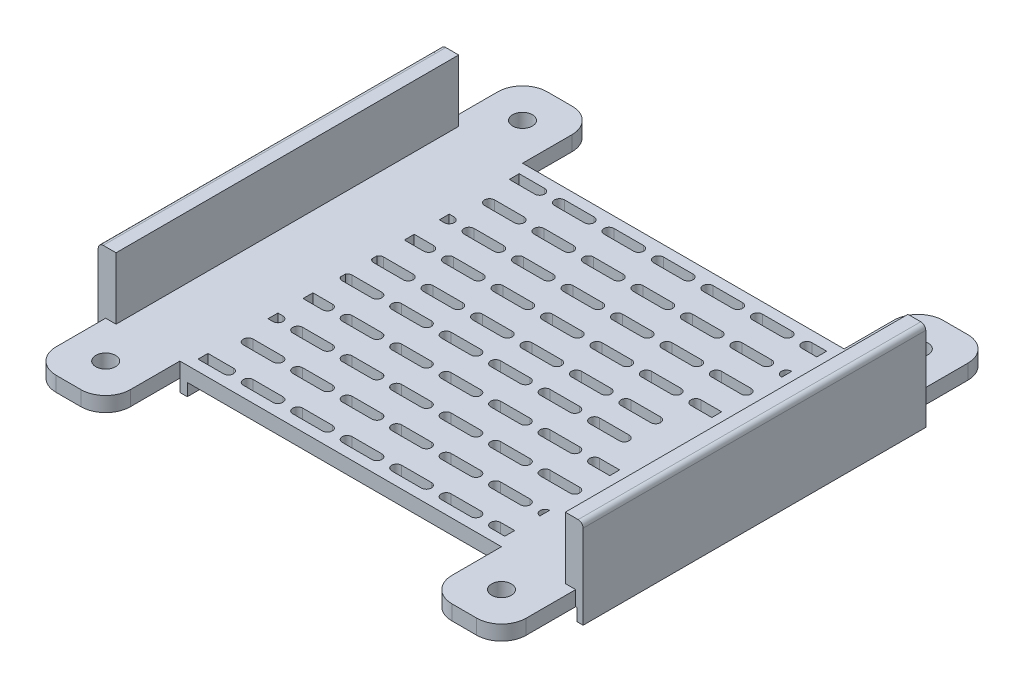
SolidWorks part; units mm, degrees
ref_plane "前视基准面" through (0, 0, 0) normal (0, 0, 1) x (1, 0, 0)
ref_plane "上视基准面" through (0, 0, 0) normal (0, 1, 0) x (1, 0, 0)
ref_plane "右视基准面" through (0, 0, 0) normal (1, 0, 0) x (0, 0, -1)
sketch "草图1" plane through (0, 0, 0) normal (0, 1, 0) x (1, 0, 0)
  line L0 (95.5, 69.25) -> (95.5, -69.25)
  line L1 (90.5, 64.25) -> (-90.5, 64.25)
  line L2 (90.5, 64.25) -> (90.5, -64.25)
  line L3 (90.5, -64.25) -> (-90.5, -64.25)
  line L4 (-90.5, 64.25) -> (-90.5, -64.25)
  line L5 (90.5, 64.25) -> (-90.5, -64.25) construction
  line L6 (90.5, -64.25) -> (-90.5, 64.25) construction
  line L7 (95.5, -69.25) -> (-95.5, -69.25)
  line L8 (-95.5, 69.25) -> (-95.5, -69.25)
  line L9 (95.5, 69.25) -> (-95.5, 69.25)
  point P0 (0, 0)
  dimension "D1" = 5
extrude "凸台-拉伸1" add sketch "草图1" along normal blind 20
sketch "草图2" plane through (0, 0, 0) normal (0, -1, 0) x (1, 0, 0)
  line L4 (-95.5, -69.25) -> (95.5, -69.25)
  line L5 (95.5, -69.25) -> (95.5, 69.25)
  line L6 (95.5, 69.25) -> (-95.5, 69.25)
  line L7 (-95.5, 69.25) -> (-95.5, -69.25)
  line L8 (-95.5, -69.25) -> (95.5, -69.25)
  line L9 (95.5, -69.25) -> (95.5, 69.25)
  line L10 (95.5, 69.25) -> (-95.5, 69.25)
  line L11 (-95.5, 69.25) -> (-95.5, -69.25)
  dimension "D1" = 0
extrude "凸台-拉伸2" add sketch "草图2" along normal blind 5
sketch "草图3" plane through (0, 0, -64.25) normal (0, 0, 1) x (1, 0, 0)
  line L4 (-90.5, 0) -> (90.5, 0)
  line L5 (90.5, 0) -> (90.5, 20)
  line L6 (90.5, 20) -> (-90.5, 20)
  line L7 (-90.5, 20) -> (-90.5, 0)
  line L8 (-90.5, 0) -> (90.5, 0)
  line L9 (90.5, 0) -> (90.5, 20)
  line L10 (90.5, 20) -> (-90.5, 20)
  line L11 (-90.5, 20) -> (-90.5, 0)
  dimension "D1" = 0
extrude "切除-拉伸1" cut sketch "草图3" against normal blind 49 and the other way blind 153
sketch "草图4" plane through (0, -5, 0) normal (0, -1, 0) x (1, 0, 0)
  line L0 (-95.5, 0) -> (-47.5, 0) construction
  line L1 (-47.5, 103) -> (47.5, 103) construction
  line L2 (-47.5, 103) -> (-47.5, -103) construction
  line L3 (-47.5, -103) -> (47.5, -103) construction
  line L4 (47.5, 103) -> (47.5, -103) construction
  line L5 (-47.5, 103) -> (47.5, -103) construction
  line L6 (-47.5, -103) -> (47.5, 103) construction
  line L7 (-95.5, 69.25) -> (-95.5, -69.25) construction
  line L8 (-95.5, 0) -> (-95.5, -35)
  line L9 (-95.5, -35) -> (-90.5, -35)
  line L10 (-90.5, -35) -> (-90.5, 35)
  line L11 (-90.5, 35) -> (-95.5, 35)
  line L12 (-95.5, 35) -> (-95.5, 0)
  line L13 (0, 0) -> (0, 35) construction
  line L14 (95.5, 35) -> (95.5, 0)
  line L15 (90.5, 35) -> (95.5, 35)
  line L16 (90.5, -35) -> (90.5, 35)
  line L17 (95.5, -35) -> (90.5, -35)
  line L18 (95.5, 0) -> (95.5, -35)
  point P0 (0, 0)
extrude "凸台-拉伸3" add sketch "草图4" along normal blind 49
sketch "草图5" plane through (0, -54, 0) normal (0, -1, 0) x (1, 0, 0)
  line L4 (-95.5, 35) -> (-95.5, -35)
  line L5 (-95.5, -35) -> (-90.5, -35)
  line L6 (-90.5, -35) -> (-90.5, 35)
  line L7 (-90.5, 35) -> (-95.5, 35)
  line L8 (-95.5, 35) -> (-95.5, -35)
  line L9 (-95.5, -35) -> (-90.5, -35)
  line L10 (-90.5, -35) -> (-90.5, 35)
  line L11 (-90.5, 35) -> (-95.5, 35)
  line L12 (95.5, 35) -> (90.5, 35)
  line L13 (90.5, 35) -> (90.5, -35)
  line L14 (90.5, -35) -> (95.5, -35)
  line L15 (95.5, -35) -> (95.5, 35)
  line L16 (95.5, 35) -> (90.5, 35)
  line L17 (90.5, 35) -> (90.5, -35)
  line L18 (90.5, -35) -> (95.5, -35)
  line L19 (95.5, -35) -> (95.5, 35)
  dimension "D1" = 0
  dimension "D2" = 0
extrude "凸台-拉伸4" add sketch "草图5" along normal blind 34
sketch "草图7" plane through (-95.5, 0, 0) normal (-1, 0, 0) x (0, 0, 1)
  line L0 (35, -88) -> (-35, -88)
  line L1 (-35, -88) -> (-35, -83)
  line L2 (-35, -88) -> (-35, -5) construction
  line L3 (-35, -83) -> (35, -83)
  line L4 (35, -88) -> (35, -5) construction
  line L5 (35, -83) -> (35, -88)
extrude "凸台-拉伸5" add sketch "草图7" along normal blind 37
sketch "草图8" plane through (95.5, 0, 0) normal (1, 0, 0) x (0, 0, -1)
  line L4 (-35, -83) -> (-35, -88)
  line L5 (35, -83) -> (-35, -83)
  line L6 (35, -88) -> (35, -83)
  line L7 (-35, -88) -> (35, -88)
  line L8 (-35, -83) -> (-35, -88)
  line L9 (35, -83) -> (-35, -83)
  line L10 (35, -88) -> (35, -83)
  line L11 (-35, -88) -> (35, -88)
  dimension "D1" = 0
extrude "凸台-拉伸6" add sketch "草图8" along normal blind 37
sketch "草图12" plane through (0, -5, 0) normal (0, -1, 0) x (1, 0, 0)
  line L0 (0, 0) -> (0, -50.9491) construction
  line L1 (0, 0) -> (21.7152, 0) construction
  line L6 (90.5, 35) -> (95.5, 35)
  line L7 (90.5, 35) -> (95.5, 35)
  line L8 (95.5, -69.25) -> (95.5, -35)
  line L9 (95.5, -35) -> (90.5, -35)
  line L10 (90.5, -35) -> (90.5, 35)
  line L11 (95.5, 35) -> (95.5, 69.25)
  line L15 (95.5, -35) -> (90.5, -35) construction
  line L16 (90.5, -35) -> (90.5, 35) construction
  line L20 (95.5, -69.25) -> (95.5, -35)
  line L27 (95.5, 35) -> (95.5, 69.25)
  line L28 (95.5, 69.25) -> (-95.5, 69.25)
  line L29 (95.5, 69.25) -> (-95.5, 69.25)
  line L30 (-95.5, 69.25) -> (-95.5, 35)
  line L31 (-95.5, 69.25) -> (-95.5, 35)
  line L32 (-95.5, 35) -> (-90.5, 35)
  line L33 (-95.5, 35) -> (-90.5, 35)
  line L34 (-90.5, 35) -> (-90.5, -35)
  line L35 (-90.5, 35) -> (-90.5, -35)
  line L36 (-90.5, -35) -> (-95.5, -35)
  line L37 (-90.5, -35) -> (-95.5, -35)
  line L38 (-95.5, -35) -> (-95.5, -69.25)
  line L39 (-95.5, -35) -> (-95.5, -69.25)
  line L40 (-95.5, -69.25) -> (95.5, -69.25)
  line L41 (-95.5, -69.25) -> (95.5, -69.25)
  circle A0 centre (48, -35) radius 12.5
  circle A1 centre (-48, -35) radius 12.5
  circle A2 centre (48, 35) radius 12.5
  circle A3 centre (-48, 35) radius 12.5
  dimension "D1" = 0
sketch "草图16" plane through (0, -88, 0) normal (0, -1, 0) x (1, 0, 0)
  line L0 (132.5, 35) -> (117.5, 35)
  line L1 (132.5, 35) -> (90.5, 35) construction
  line L2 (117.5, 35) -> (117.5, -35)
  line L3 (90.5, -35) -> (132.5, -35) construction
  line L4 (117.5, -35) -> (132.5, -35)
  line L5 (132.5, -35) -> (132.5, 35)
  line L6 (-132.5, -35) -> (-117.5, -35)
  line L7 (-132.5, -35) -> (-90.5, -35) construction
  line L8 (-117.5, -35) -> (-117.5, 35)
  line L9 (-90.5, 35) -> (-132.5, 35) construction
  line L10 (-117.5, 35) -> (-132.5, 35)
  line L11 (-132.5, 35) -> (-132.5, -35)
extrude "切除-拉伸7" cut sketch "草图16" against normal blind 62
extrude "切除-拉伸9" cut sketch "草图12" against normal blind 20 contours A0 | A1 | A3 | A2
sketch "草图19" plane through (117.5, 0, 0) normal (1, 0, 0) x (0, 0, -1)
  line L4 (-35, -83) -> (-35, -88)
  line L5 (-35, -88) -> (35, -88)
  line L6 (35, -88) -> (35, -83)
  line L7 (35, -83) -> (-35, -83)
  line L8 (-35, -83) -> (-35, -88)
  line L9 (-35, -88) -> (35, -88)
  line L10 (35, -88) -> (35, -83)
  line L11 (35, -83) -> (-35, -83)
  dimension "D1" = 0
extrude "切除-拉伸10" cut sketch "草图19" against normal blind 3.5
sketch "草图20" plane through (-117.5, 0, 0) normal (-1, 0, 0) x (0, 0, 1)
  line L4 (-35, -83) -> (-35, -88)
  line L5 (-35, -88) -> (35, -88)
  line L6 (35, -88) -> (35, -83)
  line L7 (35, -83) -> (-35, -83)
  line L8 (-35, -83) -> (-35, -88)
  line L9 (-35, -88) -> (35, -88)
  line L10 (35, -88) -> (35, -83)
  line L11 (35, -83) -> (-35, -83)
  dimension "D1" = 0
extrude "切除-拉伸11" cut sketch "草图20" against normal blind 3.5
sketch "草图21" plane through (0, -83, 0) normal (0, 1, 0) x (1, 0, 0)
  line L0 (-114, 0) -> (-95.5, 0) construction
  line L1 (-114, -35) -> (-114, 35) construction
  line L2 (-95.5, -35) -> (-95.5, 35) construction
  line L3 (-104.75, 0) -> (-104.75, -35) construction
  line L4 (-114, -35) -> (-95.5, -35) construction
  line L5 (0, 0) -> (0, 27.7926) construction
  circle A0 centre (-104.75, -17.5) radius 4
  circle A1 centre (-104.75, 17.5) radius 4
  circle A2 centre (104.75, -17.5) radius 4
  circle A3 centre (104.75, 17.5) radius 4
extrude "切除-拉伸12" cut sketch "草图21" against normal through all
fillet "圆角5" radius 10 4 edges at (114, -85.5, -35) (114, -85.5, 35) (-114, -85.5, 35) (-114, -85.5, -35)
sketch "草图22" plane through (90.5, 0, 0) normal (-1, 0, 0) x (0, 0, 1)
  line L6 (35, -88) -> (35, -5)
  line L7 (35, -5) -> (-35, -5)
  line L10 (-35, -5) -> (-35, -88)
  line L11 (-35, -88) -> (35, -88)
  line L12 (35, -88) -> (35, -5)
  line L13 (35, -5) -> (-35, -5)
  line L16 (-35, -5) -> (-35, -88)
  line L17 (-35, -88) -> (35, -88)
  dimension "D1" = 0
extrude "切除-拉伸13" cut sketch "草图22" against normal blind 54
sketch "草图23" plane through (-90.5, 0, 0) normal (1, 0, 0) x (0, 0, -1)
  line L6 (35, -5) -> (-35, -5)
  line L7 (-35, -5) -> (-35, -88)
  line L8 (-35, -88) -> (35, -88)
  line L9 (35, -88) -> (35, -5)
  line L12 (35, -5) -> (-35, -5)
  line L13 (-35, -5) -> (-35, -88)
  line L14 (-35, -88) -> (35, -88)
  line L15 (35, -88) -> (35, -5)
  dimension "D1" = 0
extrude "切除-拉伸14" cut sketch "草图23" against normal blind 54
sketch "草图24" plane through (0, -5, 0) normal (0, -1, 0) x (1, 0, 0)
  circle A1 centre (80.5, 18.25) radius 2
  circle A3 centre (80.5, -19.75) radius 2
extrude "切除-拉伸15" cut sketch "草图24" against normal blind 10
sketch "草图25" plane through (0, 0, 0) normal (0, 1, 0) x (1, 0, 0)
  circle A0 centre (80.5, -18.25) radius 4
  circle A1 centre (80.5, 19.75) radius 4
sketch "草图26" plane through (0, 0, 0) normal (0, 1, 0) x (1, 0, 0)
  line L4 (90.5, -69.25) -> (90.5, 69.25)
  line L5 (90.5, 69.25) -> (-90.5, 69.25)
  line L6 (-90.5, 69.25) -> (-90.5, -69.25)
  line L7 (-90.5, -69.25) -> (90.5, -69.25)
  line L8 (90.5, -69.25) -> (90.5, 69.25)
  line L9 (90.5, 69.25) -> (-90.5, 69.25)
  line L10 (-90.5, 69.25) -> (-90.5, -69.25)
  line L11 (-90.5, -69.25) -> (90.5, -69.25)
  circle A0 centre (48, -35) radius 12.5 construction
  circle A1 centre (48, -35) radius 12.5
  circle A2 centre (48, 35) radius 12.5 construction
  circle A3 centre (48, 35) radius 12.5
  circle A4 centre (-48, -35) radius 12.5 construction
  circle A5 centre (-48, -35) radius 12.5
  circle A6 centre (-48, 35) radius 12.5 construction
  circle A7 centre (-48, 35) radius 12.5
  dimension "D1" = 0
extrude "凸台-拉伸8" add sketch "草图26" along normal blind 1
extrude "切除-拉伸16" cut sketch "草图25" along normal blind 1 and the other way blind 4
mirror "镜向1" about plane through (0, 0, 0) normal (1, 0, 0) of "切除-拉伸15", "切除-拉伸16"
sketch "草图28" plane through (0, 1, 0) normal (0, 1, 0) x (1, 0, 0)
  circle A0 centre (-80.5, -18.25) radius 4 construction
  circle A1 centre (-80.5, -18.25) radius 4
  circle A2 centre (-80.5, 19.75) radius 4 construction
  circle A3 centre (-80.5, 19.75) radius 4
  circle A4 centre (80.5, -18.25) radius 4 construction
  circle A5 centre (80.5, -18.25) radius 4
  circle A6 centre (80.5, 19.75) radius 4 construction
  circle A7 centre (80.5, 19.75) radius 4
extrude "凸台-拉伸9" add sketch "草图28" against normal up to surface (6 mm away) up to face at (-80.5, -5, 16.25)
sketch "草图29" plane through (0, -5, 0) normal (0, -1, 0) x (1, 0, 0)
  line L0 (95.5, 69.25) -> (95, 69.25)
  line L1 (-95, 0) -> (-95, 69.25)
  line L2 (95.5, 69.25) -> (-95.5, 69.25) construction
  line L3 (-95, 69.25) -> (-95.5, 69.25)
  line L4 (-95.5, 69.25) -> (-95.5, -69.25)
  line L5 (-95.5, -69.25) -> (-95, -69.25)
  line L6 (-95.5, -69.25) -> (95.5, -69.25) construction
  line L7 (-95, -69.25) -> (-95, 0)
  line L8 (95, 69.25) -> (95, -69.25)
  line L9 (95, -69.25) -> (95.5, -69.25)
  line L10 (95.5, -69.25) -> (95.5, 69.25)
extrude "切除-拉伸18" cut sketch "草图29" against normal blind 50
sketch "草图31" plane through (0, -5, 0) normal (0, -1, 0) x (1, 0, 0)
  line L0 (-95, 69.25) -> (-95, 89.25)
  line L1 (-85, 99.25) -> (-75, 99.25)
  line L2 (-65, 89.25) -> (-65, 69.25)
  line L3 (95, 69.25) -> (-95, 69.25) construction
  line L4 (-65, 69.25) -> (-95, 69.25)
  line L5 (-80, 99.25) -> (-80, 69.25) construction
  line L6 (-80, 84.25) -> (-65, 84.25) construction
  line L7 (0, 0) -> (19.0311, 0) construction
  line L8 (0, 0) -> (0, -16.3488) construction
  line L9 (-65, -89.25) -> (-65, -69.25)
  line L10 (-85, -99.25) -> (-75, -99.25)
  line L11 (-95, -69.25) -> (-95, -89.25)
  line L12 (-65, -69.25) -> (-95, -69.25)
  line L13 (80, 84.25) -> (65, 84.25) construction
  line L14 (80, 99.25) -> (80, 69.25) construction
  line L15 (65, -69.25) -> (95, -69.25)
  line L16 (95, -69.25) -> (95, -89.25)
  line L17 (85, -99.25) -> (75, -99.25)
  line L18 (65, -89.25) -> (65, -69.25)
  line L19 (65, 69.25) -> (95, 69.25)
  line L20 (65, 89.25) -> (65, 69.25)
  line L21 (85, 99.25) -> (75, 99.25)
  line L22 (95, 69.25) -> (95, 89.25)
  arc A0 (-65, 89.25) -> (-75, 99.25) centre (-75, 89.25) ccw
  arc A1 (-95, 89.25) -> (-85, 99.25) centre (-85, 89.25) cw
  circle A2 centre (-80, 84.25) radius 4
  circle A3 centre (-80, -84.25) radius 4
  arc A4 (-65, -89.25) -> (-75, -99.25) centre (-75, -89.25) cw
  arc A5 (-95, -89.25) -> (-85, -99.25) centre (-85, -89.25) ccw
  arc A6 (95, -89.25) -> (85, -99.25) centre (85, -89.25) cw
  arc A7 (65, -89.25) -> (75, -99.25) centre (75, -89.25) ccw
  circle A8 centre (80, -84.25) radius 4
  circle A9 centre (80, 84.25) radius 4
  arc A10 (95, 89.25) -> (85, 99.25) centre (85, 89.25) ccw
  arc A11 (65, 89.25) -> (75, 99.25) centre (75, 89.25) cw
  dimension "D1" = 10
extrude "凸台-拉伸10" add sketch "草图31" against normal up to surface (6 mm away) up to face at (-48, 1, 47.5)
sketch "草图32" plane through (0, 20, 0) normal (0, 1, 0) x (1, 0, 0)
  line L0 (90.5, 69.25) -> (91.3, 69.25)
  line L4 (95, 69.25) -> (90.5, 69.25) construction
  line L5 (90.5, -69.25) -> (90.5, 69.25) construction
  line L6 (90.5, -69.25) -> (90.5, 69.25)
  line L7 (91.3, 69.25) -> (91.3, -69.25)
  line L8 (90.5, -69.25) -> (95, -69.25) construction
  line L9 (91.3, -69.25) -> (90.5, -69.25)
  line L10 (-90.5, -69.25) -> (-91.3, -69.25)
  line L11 (-95, -69.25) -> (-90.5, -69.25) construction
  line L12 (-91.3, -69.25) -> (-91.3, 69.25)
  line L13 (-90.5, 69.25) -> (-95, 69.25) construction
  line L14 (-91.3, 69.25) -> (-90.5, 69.25)
  line L15 (-90.5, 69.25) -> (-90.5, -69.25) construction
  line L16 (-90.5, 69.25) -> (-90.5, -69.25)
extrude "切除-拉伸19" cut sketch "草图32" against normal up to surface (19 mm away) up to face at (-48, 1, 47.5)
sketch "草图33" plane through (0, 20, 0) normal (0, 1, 0) x (1, 0, 0)
  line L4 (91.3, 69.25) -> (91.3, -69.25)
  line L5 (91.3, -69.25) -> (95, -69.25)
  line L6 (95, -69.25) -> (95, 69.25)
  line L7 (95, 69.25) -> (91.3, 69.25)
  line L8 (91.3, 69.25) -> (91.3, -69.25)
  line L9 (91.3, -69.25) -> (95, -69.25)
  line L10 (95, -69.25) -> (95, 69.25)
  line L11 (95, 69.25) -> (91.3, 69.25)
  line L12 (-91.3, -69.25) -> (-91.3, 69.25)
  line L13 (-91.3, 69.25) -> (-95, 69.25)
  line L14 (-95, 69.25) -> (-95, -69.25)
  line L15 (-95, -69.25) -> (-91.3, -69.25)
  line L16 (-91.3, -69.25) -> (-91.3, 69.25)
  line L17 (-91.3, 69.25) -> (-95, 69.25)
  line L18 (-95, 69.25) -> (-95, -69.25)
  line L19 (-95, -69.25) -> (-91.3, -69.25)
  dimension "D1" = 0
  dimension "D2" = 0
extrude "凸台-拉伸11" add sketch "草图33" along normal blind 6
sketch "草图34" plane through (0, -5, 0) normal (0, -1, 0) x (1, 0, 0)
  circle A0 centre (-48, -35) radius 12.5 construction
  circle A1 centre (-48, -35) radius 12.5
  circle A2 centre (-48, 35) radius 12.5 construction
  circle A3 centre (-48, 35) radius 12.5
  circle A4 centre (48, -35) radius 12.5 construction
  circle A5 centre (48, -35) radius 12.5
  circle A6 centre (48, 35) radius 12.5 construction
  circle A7 centre (48, 35) radius 12.5
extrude "凸台-拉伸12" add sketch "草图34" against normal up to surface (6 mm away) up to face at (0, 1, 0)
sketch "草图35" plane through (0, -5, 0) normal (0, -1, 0) x (1, 0, 0)
  line L0 (65, -69.25) -> (62, -69.25)
  line L2 (65, 69.25) -> (65, -69.25)
  line L6 (-65, -69.25) -> (65, -69.25) construction
  line L8 (62, -69.25) -> (62, 69.25)
  line L9 (65, 69.25) -> (-65, 69.25) construction
  line L10 (62, 69.25) -> (65, 69.25)
  line L11 (-65, -69.25) -> (-62, -69.25)
  line L12 (-62, -69.25) -> (-62, 69.25)
  line L13 (-62, 69.25) -> (-65, 69.25)
  line L14 (-65, 69.25) -> (-65, 89.25) construction
  line L15 (-65, 69.25) -> (-65, -69.25)
  point P0 (0, 0)
extrude "凸台-拉伸13" add sketch "草图35" along normal blind 5
sketch "草图36" plane through (-95, 0, 0) normal (-1, 0, 0) x (0, 0, 1)
  line L0 (-69.25, -10) -> (-69.25, -5) construction
  line L1 (-69.25, -10) -> (-69.25, -5)
  line L2 (69.25, -10) -> (69.25, -5) construction
  line L3 (69.25, -10) -> (69.25, -5)
  line L7 (-69.25, 26) -> (69.25, 26) construction
  line L8 (-69.25, 26) -> (69.25, 26)
  line L9 (69.25, 26) -> (69.25, 1) construction
  line L10 (69.25, 26) -> (69.25, 1)
  line L13 (-69.25, -10) -> (69.25, -10)
  line L16 (-69.25, 26) -> (-69.25, 1) construction
  line L17 (-69.25, 26) -> (-69.25, 1)
  line L18 (-69.25, 1) -> (-69.25, -5)
  line L19 (69.25, -5) -> (69.25, 1)
extrude "凸台-拉伸14" add sketch "草图36" along normal blind 3
sketch "草图37" plane through (-95, 0, 0) normal (1, 0, 0) x (0, 0, -1)
  line L4 (69.25, -5) -> (-69.25, -5)
  line L5 (-69.25, -5) -> (-69.25, -10)
  line L6 (-69.25, -10) -> (69.25, -10)
  line L7 (69.25, -10) -> (69.25, -5)
  line L8 (69.25, -5) -> (-69.25, -5)
  line L9 (-69.25, -5) -> (-69.25, -10)
  line L10 (-69.25, -10) -> (69.25, -10)
  line L11 (69.25, -10) -> (69.25, -5)
  dimension "D1" = 0
extrude "切除-拉伸20" cut sketch "草图37" against normal blind 0.5
mirror "镜向2" about plane through (0, 0, 0) normal (1, 0, 0) of "切除-拉伸20", "凸台-拉伸14"
sketch "草图38" plane through (0, -5, 0) normal (0, -1, 0) x (1, 0, 0)
  line L2 (0, 0) -> (62, 0)
  line L3 (62, 69.25) -> (62, -69.25) construction
  line L4 (0, -2.5) -> (-62, -2.5)
  line L5 (0, -2.5) -> (62, -2.5)
  line L6 (0, 2.5) -> (-62, 2.5)
  line L7 (0, 2.5) -> (62, 2.5)
  line L8 (-62, -69.25) -> (-62, 69.25) construction
  line L9 (-62, -2.5) -> (-62, 2.5)
  line L10 (62, 69.25) -> (62, -69.25) construction
  line L11 (62, 2.5) -> (62, -2.5)
  line L12 (0, 0) -> (-62, 0) construction
  dimension "D1" = 2.5
  dimension "D2" = 2.5
extrude "凸台-拉伸15" add sketch "草图38" along normal up to surface (5 mm away) contours L6 L9 L4 L5 L11 L7 up to face at (-63.5, -10, 0)
sketch "草图40" plane through (0, -5, 0) normal (0, -1, 0) x (1, 0, 0)
  line L0 (0, 0) -> (0, 69.25) construction
  line L1 (62, 69.25) -> (-62, 69.25) construction
  line L2 (0, 34.625) -> (-12, 34.625) construction
  line L3 (0, 34.625) -> (-32.125, 2.5) construction
  line L4 (0, 32.625) -> (-12, 32.625)
  line L5 (0, 36.625) -> (-12, 36.625)
  line L6 (62, 2.5) -> (-62, 2.5) construction
  line L7 (25, 34.625) -> (13, 34.625) construction
  line L8 (25, 32.625) -> (13, 32.625)
  line L9 (25, 36.625) -> (13, 36.625)
  line L10 (50, 34.625) -> (38, 34.625) construction
  line L11 (50, 32.625) -> (38, 32.625)
  line L12 (50, 36.625) -> (38, 36.625)
  line L13 (-25, 34.625) -> (-37, 34.625) construction
  line L14 (-25, 32.625) -> (-37, 32.625)
  line L15 (-25, 36.625) -> (-37, 36.625)
  arc A0 (0, 32.625) -> (0, 36.625) centre (0, 34.625) ccw
  arc A1 (-12, 36.625) -> (-12, 32.625) centre (-12, 34.625) ccw
  arc A2 (25, 32.625) -> (25, 36.625) centre (25, 34.625) ccw
  arc A3 (13, 36.625) -> (13, 32.625) centre (13, 34.625) ccw
  arc A4 (50, 32.625) -> (50, 36.625) centre (50, 34.625) ccw
  arc A5 (38, 36.625) -> (38, 32.625) centre (38, 34.625) ccw
  arc A6 (-25, 32.625) -> (-25, 36.625) centre (-25, 34.625) ccw
  arc A7 (-37, 36.625) -> (-37, 32.625) centre (-37, 34.625) ccw
  point P9 (-6, 34.625)
  point P20 (19, 34.625)
  point P27 (44, 34.625)
  point P34 (-31, 34.625)
  dimension "D1" = 45
  dimension "D2" = 3
  dimension "D3" = 2
extrude "切除-拉伸22" cut sketch "草图40" against normal through all contours L5 A1 L4 A0
sketch "草图41" plane through (0, -5, 0) normal (0, -1, 0) x (1, 0, 0)
  line L0 (0, 0) -> (0, 69.25)
  line L1 (62, 69.25) -> (-62, 69.25) construction
  line L2 (0, 34.625) -> (-32.125, 2.5)
  line L3 (62, 2.5) -> (-62, 2.5) construction
  dimension "D1" = 45
pattern_linear "阵列(线性)1" count 3 spacing 20 along (-0.7071, 0, -0.7071) of "切除-拉伸22"
pattern_linear "阵列(线性)2" count 3 spacing 20 along (0.7071, 0, 0.7071) of "切除-拉伸22"
pattern_linear "阵列(线性)3" count 5 spacing 20 along (1, 0, 0) of "阵列(线性)2", "阵列(线性)1", "切除-拉伸22"
sketch "草图42" plane through (0, 1, 0) normal (0, 1, 0) x (1, 0, 0)
  line L0 (82.1421, -50.7671) -> (91.3, -50.7671) construction
  line L1 (82.1421, -50.7671) -> (91.3, -50.7671)
  line L2 (82.1421, -46.7671) -> (91.3, -46.7671) construction
  line L3 (82.1421, -46.7671) -> (91.3, -46.7671)
  line L4 (94.1421, -46.7671) -> (91.3, -46.7671) construction
  line L5 (94.1421, -46.7671) -> (91.3, -46.7671)
  line L6 (94.1421, -50.7671) -> (91.3, -50.7671) construction
  line L7 (94.1421, -50.7671) -> (91.3, -50.7671)
  line L8 (98, -64.9093) -> (96.2843, -64.9093) construction
  line L9 (98, -64.9093) -> (96.2843, -64.9093)
  line L10 (98, -60.9093) -> (96.2843, -60.9093) construction
  line L11 (98, -60.9093) -> (96.2843, -60.9093)
  line L12 (98, -64.9093) -> (98, -60.9093) construction
  line L13 (98, -64.9093) -> (98, -60.9093)
  line L14 (76.2843, -60.9093) -> (88.2843, -60.9093) construction
  line L15 (76.2843, -60.9093) -> (88.2843, -60.9093)
  line L16 (76.2843, -64.9093) -> (88.2843, -64.9093) construction
  line L17 (76.2843, -64.9093) -> (88.2843, -64.9093)
  line L20 (56.2843, -60.9093) -> (68.2843, -60.9093) construction
  line L21 (65, -60.9093) -> (68.2843, -60.9093)
  line L22 (56.2843, -64.9093) -> (68.2843, -64.9093) construction
  line L23 (65, -64.9093) -> (68.2843, -64.9093)
  line L26 (62.1421, -50.7671) -> (74.1421, -50.7671) construction
  line L27 (62.1421, -46.7671) -> (74.1421, -46.7671) construction
  line L28 (65, -50.7671) -> (74.1421, -50.7671)
  line L29 (65, -46.7671) -> (74.1421, -46.7671)
  line L30 (68, -32.625) -> (80, -32.625) construction
  line L31 (68, -36.625) -> (80, -36.625) construction
  line L32 (68, -32.625) -> (80, -32.625)
  line L33 (68, -36.625) -> (80, -36.625)
  line L34 (53.8579, -22.4829) -> (65.8579, -22.4829) construction
  line L35 (53.8579, -18.4829) -> (65.8579, -18.4829) construction
  line L37 (65, -22.4829) -> (65.8579, -22.4829)
  line L38 (65, -18.4829) -> (65.8579, -18.4829)
  line L44 (62, -64.9093) -> (65, -64.9093)
  line L45 (65, -64.9093) -> (65, -60.9093)
  line L46 (65, -60.9093) -> (62, -60.9093)
  line L47 (62, -60.9093) -> (62, -64.9093)
  line L48 (62, -64.9093) -> (65, -64.9093)
  line L49 (62.1421, -50.7671) -> (65, -50.7671)
  line L50 (65, -60.9093) -> (62, -60.9093)
  line L51 (62, -60.9093) -> (62, -64.9093)
  line L52 (65, -50.7671) -> (65, -46.7671)
  line L53 (65, -46.7671) -> (62.1421, -46.7671)
  line L54 (62, -46.7722) -> (62, -50.7621)
  line L55 (62.1421, -50.7671) -> (65, -50.7671)
  line L56 (62, -22.4829) -> (65, -22.4829)
  line L57 (65, -46.7671) -> (62.1421, -46.7671)
  line L58 (62, -46.7722) -> (62, -50.7621)
  line L59 (65, -22.4829) -> (65, -18.4829)
  line L60 (65, -18.4829) -> (62, -18.4829)
  line L61 (62, -18.4829) -> (62, -22.4829)
  line L62 (62, -22.4829) -> (65, -22.4829)
  line L64 (65, -18.4829) -> (62, -18.4829)
  line L65 (62, -18.4829) -> (62, -22.4829)
  arc A0 (82.1421, -46.7671) -> (82.1421, -50.7671) centre (82.1421, -48.7671) ccw construction
  arc A1 (82.1421, -46.7671) -> (82.1421, -50.7671) centre (82.1421, -48.7671) ccw
  arc A2 (95.5, -50.2355) -> (95.5, -47.2987) centre (94.1421, -48.7671) ccw construction
  arc A3 (95.5, -50.2355) -> (95.5, -47.2987) centre (94.1421, -48.7671) ccw
  arc A4 (95.5, -47.2987) -> (94.1421, -46.7671) centre (94.1421, -48.7671) ccw construction
  arc A5 (95.5, -47.2987) -> (94.1421, -46.7671) centre (94.1421, -48.7671) ccw
  arc A6 (94.1421, -50.7671) -> (95.5, -50.2355) centre (94.1421, -48.7671) ccw construction
  arc A7 (94.1421, -50.7671) -> (95.5, -50.2355) centre (94.1421, -48.7671) ccw
  arc A8 (96.2843, -60.9093) -> (96.2843, -64.9093) centre (96.2843, -62.9093) ccw construction
  arc A9 (96.2843, -60.9093) -> (96.2843, -64.9093) centre (96.2843, -62.9093) ccw
  arc A10 (88.2843, -64.9093) -> (88.2843, -60.9093) centre (88.2843, -62.9093) ccw construction
  arc A11 (88.2843, -64.9093) -> (88.2843, -60.9093) centre (88.2843, -62.9093) ccw
  arc A12 (76.2843, -60.9093) -> (76.2843, -64.9093) centre (76.2843, -62.9093) ccw construction
  arc A13 (76.2843, -60.9093) -> (76.2843, -64.9093) centre (76.2843, -62.9093) ccw
  arc A14 (68.2843, -64.9093) -> (68.2843, -60.9093) centre (68.2843, -62.9093) ccw construction
  arc A15 (68.2843, -64.9093) -> (68.2843, -60.9093) centre (68.2843, -62.9093) ccw
  arc A16 (74.1421, -50.7671) -> (74.1421, -46.7671) centre (74.1421, -48.7671) ccw construction
  arc A17 (74.1421, -50.7671) -> (74.1421, -46.7671) centre (74.1421, -48.7671) ccw
  arc A18 (68, -32.625) -> (68, -36.625) centre (68, -34.625) ccw construction
  arc A19 (80, -36.625) -> (80, -32.625) centre (80, -34.625) ccw construction
  arc A20 (68, -32.625) -> (68, -36.625) centre (68, -34.625) ccw
  arc A21 (80, -36.625) -> (80, -32.625) centre (80, -34.625) ccw
  arc A22 (65.8579, -22.4829) -> (65.8579, -18.4829) centre (65.8579, -20.4829) ccw construction
  arc A23 (65.8579, -22.4829) -> (65.8579, -18.4829) centre (65.8579, -20.4829) ccw
  arc A26 (62, -50.7621) -> (62.1421, -50.7671) centre (62.1421, -48.7671) ccw
  arc A27 (62.1421, -46.7671) -> (62, -46.7722) centre (62.1421, -48.7671) ccw
  arc A28 (62, -50.7621) -> (62.1421, -50.7671) centre (62.1421, -48.7671) ccw
  arc A29 (62.1421, -46.7671) -> (62, -46.7722) centre (62.1421, -48.7671) ccw
  dimension "D1" = 0
  dimension "D2" = 0
  dimension "D3" = 0
extrude "凸台-拉伸16" add sketch "草图42" against normal up to surface (6 mm away) up to face at (63.5, -5, 62.9093)
sketch "草图43" plane through (0, 1, 0) normal (0, 1, 0) x (1, 0, 0)
  line L0 (94.1421, -46.7671) -> (91.3, -46.7671) construction
  line L1 (94.1421, -46.7671) -> (91.3, -46.7671)
  line L2 (94.1421, -50.7671) -> (91.3, -50.7671) construction
  line L3 (96.2843, -64.9093) -> (98, -64.9093)
  line L4 (98, -64.9093) -> (98, -60.9093)
  line L5 (98, -60.9093) -> (96.2843, -60.9093)
  line L6 (96.2843, -64.9093) -> (98, -64.9093)
  line L7 (98, -64.9093) -> (98, -60.9093)
  line L8 (98, -60.9093) -> (96.2843, -60.9093)
  line L9 (94.1421, -50.7671) -> (91.3, -50.7671)
  line L10 (91.3, -50.7671) -> (91.3, -46.7671)
  arc A0 (94.1421, -50.7671) -> (94.1421, -46.7671) centre (94.1421, -48.7671) ccw construction
  arc A1 (96.2843, -60.9093) -> (96.2843, -64.9093) centre (96.2843, -62.9093) ccw
  arc A2 (96.2843, -60.9093) -> (96.2843, -64.9093) centre (96.2843, -62.9093) ccw
  arc A3 (94.1421, -50.7671) -> (94.1421, -46.7671) centre (94.1421, -48.7671) ccw
  dimension "D1" = 0
extrude "凸台-拉伸17" add sketch "草图43" along normal up to surface (25 mm away)
pattern_linear "阵列(线性)4" count 5 spacing 20 along (-1, 0, 0) of "阵列(线性)1", "阵列(线性)2", "切除-拉伸22"
sketch "草图44" plane through (0, 1, 0) normal (0, 1, 0) x (1, 0, 0)
  line L0 (-63.7157, -64.9093) -> (-51.7157, -64.9093) construction
  line L1 (-63.7157, -60.9093) -> (-51.7157, -60.9093) construction
  line L2 (-62, -60.9093) -> (-62, -64.9093) construction
  line L3 (-62, -32.625) -> (-62, -36.625) construction
  line L4 (-72, -32.625) -> (-60, -32.625) construction
  line L5 (-72, -36.625) -> (-60, -36.625) construction
  line L7 (-77.8579, -50.7671) -> (-65.8579, -50.7671) construction
  line L8 (-77.8579, -46.7671) -> (-65.8579, -46.7671) construction
  line L9 (-63.7157, -64.9093) -> (-62, -64.9093)
  line L10 (-63.7157, -60.9093) -> (-62, -60.9093)
  line L11 (-62, -60.9093) -> (-62, -64.9093)
  line L12 (-62, -32.625) -> (-62, -36.625)
  line L13 (-72, -32.625) -> (-62, -32.625)
  line L14 (-72, -36.625) -> (-62, -36.625)
  line L16 (-77.8579, -50.7671) -> (-65.8579, -50.7671)
  line L17 (-77.8579, -46.7671) -> (-65.8579, -46.7671)
  line L18 (-98, -4.3407) -> (-98, -8.3407) construction
  line L19 (-62, -18.4829) -> (-62, -22.4829) construction
  line L20 (-66.1421, -22.4829) -> (-54.1421, -22.4829) construction
  line L21 (-66.1421, -18.4829) -> (-54.1421, -18.4829) construction
  line L22 (-62, -5.313) -> (-62, -7.3685) construction
  line L23 (-80.2843, -8.3407) -> (-68.2843, -8.3407) construction
  line L24 (-80.2843, -4.3407) -> (-68.2843, -4.3407) construction
  line L25 (-91.3, -8.3407) -> (-88.2843, -8.3407) construction
  line L26 (-91.3, -4.3407) -> (-88.2843, -4.3407) construction
  line L27 (-91.3, -4.3407) -> (-98, -4.3407) construction
  line L28 (-91.3, -8.3407) -> (-98, -8.3407) construction
  line L29 (-98, -4.3407) -> (-98, -8.3407)
  line L30 (-91.3, -8.3407) -> (-98, -8.3407)
  line L31 (-91.3, -4.3407) -> (-98, -4.3407)
  line L32 (-91.3, -4.3407) -> (-88.2843, -4.3407)
  line L33 (-91.3, -8.3407) -> (-88.2843, -8.3407)
  line L34 (-80.2843, -4.3407) -> (-68.2843, -4.3407)
  line L35 (-80.2843, -8.3407) -> (-68.2843, -8.3407)
  line L36 (-62, -5.313) -> (-62, -7.3685)
  line L37 (-66.1421, -18.4829) -> (-62, -18.4829)
  line L38 (-66.1421, -22.4829) -> (-62, -22.4829)
  line L39 (-62, -18.4829) -> (-62, -22.4829)
  line L40 (-91.3, -36.625) -> (-80, -36.625) construction
  line L41 (-92, -36.625) -> (-91.3, -36.625) construction
  line L42 (-92, -32.625) -> (-91.3, -32.625) construction
  line L43 (-91.3, -32.625) -> (-80, -32.625) construction
  line L44 (-86.1421, -22.4829) -> (-74.1421, -22.4829) construction
  line L45 (-86.1421, -18.4829) -> (-74.1421, -18.4829) construction
  line L46 (-94.1421, -22.4829) -> (-98, -22.4829) construction
  line L47 (-94.1421, -18.4829) -> (-98, -18.4829) construction
  line L48 (-98, -18.4829) -> (-98, -22.4829) construction
  line L49 (-91.3, -36.625) -> (-80, -36.625)
  line L50 (-92, -36.625) -> (-91.3, -36.625)
  line L51 (-92, -32.625) -> (-91.3, -32.625)
  line L52 (-91.3, -32.625) -> (-80, -32.625)
  line L53 (-86.1421, -22.4829) -> (-74.1421, -22.4829)
  line L54 (-86.1421, -18.4829) -> (-74.1421, -18.4829)
  line L55 (-94.1421, -22.4829) -> (-98, -22.4829)
  line L56 (-94.1421, -18.4829) -> (-98, -18.4829)
  line L57 (-98, -18.4829) -> (-98, -22.4829)
  arc A0 (-63.7157, -60.9093) -> (-63.7157, -64.9093) centre (-63.7157, -62.9093) ccw construction
  arc A1 (-72, -32.625) -> (-72, -36.625) centre (-72, -34.625) ccw construction
  arc A2 (-65.8579, -50.7671) -> (-65.8579, -46.7671) centre (-65.8579, -48.7671) ccw construction
  arc A3 (-77.8579, -46.7671) -> (-77.8579, -50.7671) centre (-77.8579, -48.7671) ccw construction
  arc A4 (-63.7157, -60.9093) -> (-63.7157, -64.9093) centre (-63.7157, -62.9093) ccw
  arc A5 (-72, -32.625) -> (-72, -36.625) centre (-72, -34.625) ccw
  arc A7 (-77.8579, -46.7671) -> (-77.8579, -50.7671) centre (-77.8579, -48.7671) ccw
  arc A8 (-66.1421, -18.4829) -> (-66.1421, -22.4829) centre (-66.1421, -20.4829) ccw construction
  arc A9 (-60.2843, -4.3407) -> (-60.2843, -8.3407) centre (-60.2843, -6.3407) ccw construction
  arc A10 (-68.2843, -8.3407) -> (-68.2843, -4.3407) centre (-68.2843, -6.3407) ccw construction
  arc A11 (-80.2843, -4.3407) -> (-80.2843, -8.3407) centre (-80.2843, -6.3407) ccw construction
  arc A12 (-88.2843, -8.3407) -> (-88.2843, -4.3407) centre (-88.2843, -6.3407) ccw construction
  arc A13 (-88.2843, -8.3407) -> (-88.2843, -4.3407) centre (-88.2843, -6.3407) ccw
  arc A14 (-80.2843, -4.3407) -> (-80.2843, -8.3407) centre (-80.2843, -6.3407) ccw
  arc A15 (-68.2843, -8.3407) -> (-68.2843, -4.3407) centre (-68.2843, -6.3407) ccw
  arc A16 (-62, -5.313) -> (-62, -7.3685) centre (-60.2843, -6.3407) ccw
  arc A17 (-66.1421, -18.4829) -> (-66.1421, -22.4829) centre (-66.1421, -20.4829) ccw
  arc A18 (-80, -36.625) -> (-80, -32.625) centre (-80, -34.625) ccw construction
  arc A19 (-92, -32.625) -> (-92, -36.625) centre (-92, -34.625) ccw construction
  arc A20 (-74.1421, -22.4829) -> (-74.1421, -18.4829) centre (-74.1421, -20.4829) ccw construction
  arc A21 (-86.1421, -18.4829) -> (-86.1421, -22.4829) centre (-86.1421, -20.4829) ccw construction
  arc A22 (-94.1421, -22.4829) -> (-94.1421, -18.4829) centre (-94.1421, -20.4829) ccw construction
  arc A23 (-80, -36.625) -> (-80, -32.625) centre (-80, -34.625) ccw
  arc A24 (-92, -32.625) -> (-92, -36.625) centre (-92, -34.625) ccw
  arc A25 (-74.1421, -22.4829) -> (-74.1421, -18.4829) centre (-74.1421, -20.4829) ccw
  arc A26 (-86.1421, -18.4829) -> (-86.1421, -22.4829) centre (-86.1421, -20.4829) ccw
  arc A27 (-94.1421, -22.4829) -> (-94.1421, -18.4829) centre (-94.1421, -20.4829) ccw
  arc A29 (-65.8579, -50.7671) -> (-65.8579, -46.7671) centre (-65.8579, -48.7671) ccw
extrude "凸台-拉伸18" add sketch "草图44" against normal up to surface (6 mm away)
sketch "草图45" plane through (0, 1, 0) normal (0, 1, 0) x (1, 0, 0)
  line L0 (-91.3, -4.3407) -> (-98, -4.3407) construction
  line L1 (-91.3, -4.3407) -> (-98, -4.3407)
  line L2 (-91.3, -8.3407) -> (-98, -8.3407) construction
  line L3 (-91.3, -8.3407) -> (-98, -8.3407)
  line L4 (-98, -4.3407) -> (-98, -8.3407) construction
  line L5 (-98, -4.3407) -> (-98, -8.3407)
  line L6 (-92, -32.625) -> (-91.3, -32.625) construction
  line L7 (-92, -32.625) -> (-91.3, -32.625)
  line L8 (-92, -36.625) -> (-91.3, -36.625) construction
  line L9 (-94.1421, -18.4829) -> (-98, -18.4829)
  line L10 (-98, -18.4829) -> (-98, -22.4829)
  line L11 (-98, -22.4829) -> (-94.1421, -22.4829)
  line L12 (-94.1421, -18.4829) -> (-98, -18.4829)
  line L13 (-98, -18.4829) -> (-98, -22.4829)
  line L14 (-98, -22.4829) -> (-94.1421, -22.4829)
  line L15 (-92, -36.625) -> (-91.3, -36.625)
  line L16 (-91.3, -8.3407) -> (-91.3, -4.3407)
  line L17 (-91.3, -32.625) -> (-91.3, -36.625)
  arc A0 (-92, -32.625) -> (-92, -36.625) centre (-92, -34.625) ccw construction
  arc A1 (-94.1421, -22.4829) -> (-94.1421, -18.4829) centre (-94.1421, -20.4829) ccw
  arc A2 (-94.1421, -22.4829) -> (-94.1421, -18.4829) centre (-94.1421, -20.4829) ccw
  arc A3 (-92, -32.625) -> (-92, -36.625) centre (-92, -34.625) ccw
  dimension "D1" = 0
extrude "凸台-拉伸19" add sketch "草图45" along normal up to surface (25 mm away) up to face at (-94.65, 26, -32.4546)
mirror "镜向5" about plane through (0, 0, 0) normal (0, 0, 1) of "阵列(线性)4", "阵列(线性)3", "阵列(线性)2", "阵列(线性)1", "切除-拉伸22"
sketch "草图46" plane through (0, 1, 0) normal (0, 1, 0) x (1, 0, 0)
  line L10 (62.2843, 60.9093) -> (62.2843, 69.25)
  line L11 (56.2843, 60.9093) -> (68.2843, 60.9093) construction
  line L12 (65, 69.25) -> (-65, 69.25) construction
  line L13 (98, 64.9093) -> (98, 69.25) construction
  line L14 (98, 64.9093) -> (98, 69.25)
  line L15 (62.2843, 69.25) -> (98, 69.25)
  line L16 (62.2843, 60.9093) -> (62.2843, 4.433)
  line L17 (62.2843, 4.433) -> (98, 4.433)
  line L18 (98, 4.433) -> (98, 64.9093)
  line L19 (0, 0) -> (0, 15.6294) construction
  line L20 (-62.2843, 4.433) -> (-98, 4.433)
  line L21 (-62.2843, 60.9093) -> (-62.2843, 4.433)
  line L22 (-62.2843, 60.9093) -> (-62.2843, 69.25)
  line L23 (-62.2843, 69.25) -> (-98, 69.25)
  line L24 (-98, 64.9093) -> (-98, 69.25)
  line L25 (-98, 4.433) -> (-98, 64.9093)
extrude "凸台-拉伸20" add sketch "草图46" against normal up to surface (6 mm away) up to face at (-34.2843, -5, -6.3407)
sketch "草图47" plane through (0, 1, 0) normal (0, 1, 0) x (1, 0, 0)
  line L0 (-98, 4.433) -> (-98, 4.3407) construction
  line L1 (-62, 5.313) -> (-62, 7.3685)
  line L2 (-62, 5.313) -> (-62, 7.3685)
  line L3 (-98, 4.433) -> (-98, 4.3407)
  line L4 (-62, 22.4829) -> (-62.2843, 22.4829)
  line L5 (-62.2843, 22.4829) -> (-62.2843, 18.4829)
  line L6 (-62.2843, 18.4829) -> (-62, 18.4829)
  line L7 (-62, 18.4829) -> (-62, 22.4829)
  line L8 (-62, 22.4829) -> (-62.2843, 22.4829)
  line L9 (-62.2843, 22.4829) -> (-62.2843, 18.4829)
  line L10 (-62.2843, 18.4829) -> (-62, 18.4829)
  line L11 (-62, 18.4829) -> (-62, 22.4829)
  line L12 (-98, 4.433) -> (-87.6837, 4.433) construction
  line L13 (-98, 4.433) -> (-87.6837, 4.433)
  line L14 (-62, 36.625) -> (-62.2843, 36.625)
  line L15 (-62.2843, 36.625) -> (-62.2843, 32.625)
  line L16 (-62.2843, 32.625) -> (-62, 32.625)
  line L17 (-62, 32.625) -> (-62, 36.625)
  line L18 (-62, 36.625) -> (-62.2843, 36.625)
  line L19 (-62.2843, 36.625) -> (-62.2843, 32.625)
  line L20 (-62.2843, 32.625) -> (-62, 32.625)
  line L21 (-62, 32.625) -> (-62, 36.625)
  line L22 (-62, 64.9093) -> (-62.2843, 64.9093)
  line L23 (-62.2843, 64.9093) -> (-62.2843, 60.9093)
  line L24 (-62.2843, 60.9093) -> (-62, 60.9093)
  line L25 (-62, 60.9093) -> (-62, 64.9093)
  line L26 (-62, 64.9093) -> (-62.2843, 64.9093)
  line L27 (-62.2843, 64.9093) -> (-62.2843, 60.9093)
  line L28 (-62.2843, 60.9093) -> (-62, 60.9093)
  line L29 (-62, 60.9093) -> (-62, 64.9093)
  line L30 (-91.3, 4.3407) -> (-88.2843, 4.3407) construction
  line L31 (-91.3, 4.3407) -> (-88.2843, 4.3407)
  line L32 (-91.3, 4.3407) -> (-98, 4.3407) construction
  line L33 (-91.3, 4.3407) -> (-98, 4.3407)
  line L34 (-80.8849, 4.433) -> (-67.6837, 4.433) construction
  line L35 (-80.8849, 4.433) -> (-67.6837, 4.433)
  line L36 (-80.2843, 4.3407) -> (-68.2843, 4.3407) construction
  line L37 (-80.2843, 4.3407) -> (-68.2843, 4.3407)
  arc A0 (-88.2843, 4.3407) -> (-87.6837, 4.433) centre (-88.2843, 6.3407) ccw construction
  arc A1 (-62, 7.3685) -> (-62, 5.313) centre (-60.2843, 6.3407) ccw
  arc A2 (-62, 7.3685) -> (-62, 5.313) centre (-60.2843, 6.3407) ccw
  arc A3 (-88.2843, 4.3407) -> (-87.6837, 4.433) centre (-88.2843, 6.3407) ccw
  arc A4 (-68.2843, 4.3407) -> (-67.6837, 4.433) centre (-68.2843, 6.3407) ccw construction
  arc A5 (-68.2843, 4.3407) -> (-67.6837, 4.433) centre (-68.2843, 6.3407) ccw
  arc A6 (-80.8849, 4.433) -> (-80.2843, 4.3407) centre (-80.2843, 6.3407) ccw construction
  arc A7 (-80.8849, 4.433) -> (-80.2843, 4.3407) centre (-80.2843, 6.3407) ccw
  dimension "D1" = 0
  dimension "D2" = 0
  dimension "D3" = 0
  dimension "D4" = 0
extrude "凸台-拉伸21" add sketch "草图47" against normal up to surface (6 mm away) up to face at (-62.1421, -5, -20.4829)
sketch "草图48" plane through (0, 1, 0) normal (0, 1, 0) x (1, 0, 0)
  line L0 (-91.3, 36.625) -> (-92, 36.625) construction
  line L1 (-91.3, 36.625) -> (-92, 36.625)
  line L2 (-92, 32.625) -> (-91.3, 32.625) construction
  line L3 (-94.1421, 22.4829) -> (-98, 22.4829)
  line L4 (-98, 22.4829) -> (-98, 18.4829)
  line L5 (-98, 18.4829) -> (-94.1421, 18.4829)
  line L6 (-94.1421, 22.4829) -> (-98, 22.4829)
  line L7 (-98, 22.4829) -> (-98, 18.4829)
  line L8 (-98, 18.4829) -> (-94.1421, 18.4829)
  line L9 (-92, 32.625) -> (-91.3, 32.625)
  line L10 (-91.3, 8.3407) -> (-98, 8.3407) construction
  line L11 (-91.3, 8.3407) -> (-98, 8.3407)
  line L12 (-98, 8.3407) -> (-98, 4.3407) construction
  line L13 (-98, 8.3407) -> (-98, 4.3407)
  line L14 (-91.3, 4.3407) -> (-98, 4.3407) construction
  line L15 (-91.3, 4.3407) -> (-98, 4.3407)
  line L16 (94.1421, 50.7671) -> (91.3, 50.7671) construction
  line L17 (94.1421, 50.7671) -> (91.3, 50.7671)
  line L18 (94.1421, 46.7671) -> (91.3, 46.7671) construction
  line L19 (98, 60.9093) -> (98, 64.9093)
  line L20 (98, 64.9093) -> (96.2843, 64.9093)
  line L21 (96.2843, 60.9093) -> (98, 60.9093)
  line L22 (98, 60.9093) -> (98, 64.9093)
  line L23 (98, 64.9093) -> (96.2843, 64.9093)
  line L24 (96.2843, 60.9093) -> (98, 60.9093)
  line L25 (94.1421, 46.7671) -> (91.3, 46.7671)
  line L26 (91.3, 46.7671) -> (91.3, 50.7671)
  line L27 (-91.3, 4.3407) -> (-91.3, 8.3407)
  line L28 (-91.3, 32.625) -> (-91.3, 36.625)
  arc A0 (-92, 36.625) -> (-92, 32.625) centre (-92, 34.625) ccw construction
  arc A1 (-94.1421, 18.4829) -> (-94.1421, 22.4829) centre (-94.1421, 20.4829) ccw
  arc A2 (-94.1421, 18.4829) -> (-94.1421, 22.4829) centre (-94.1421, 20.4829) ccw
  arc A3 (-92, 36.625) -> (-92, 32.625) centre (-92, 34.625) ccw
  arc A4 (94.1421, 46.7671) -> (94.1421, 50.7671) centre (94.1421, 48.7671) ccw construction
  arc A5 (96.2843, 64.9093) -> (96.2843, 60.9093) centre (96.2843, 62.9093) ccw
  arc A6 (96.2843, 64.9093) -> (96.2843, 60.9093) centre (96.2843, 62.9093) ccw
  arc A7 (94.1421, 46.7671) -> (94.1421, 50.7671) centre (94.1421, 48.7671) ccw
  dimension "D1" = 0
  dimension "D2" = 0
extrude "凸台-拉伸22" add sketch "草图48" along normal up to surface (25 mm away) up to face at (-94.65, 26, 32.4546)
fillet "圆角6" radius 2 2 edges at (-98, 26, 0) (98, 26, 0)
sketch "草图49" plane through (0, 26, 0) normal (0, 1, 0) x (1, 0, 0)
  line L0 (-91.3, -69.25) -> (-90.8, -69.25)
  line L1 (-91.3, 69.25) -> (-90.8, 69.25)
  line L2 (-90.8, 69.25) -> (-90.8, -69.25)
  line L3 (-91.3, -69.25) -> (-91.3, 69.25) construction
  line L4 (-91.3, -69.25) -> (-91.3, 69.25)
  line L5 (0, 0) -> (0, 30.0446) construction
  line L6 (91.3, -69.25) -> (91.3, 69.25)
  line L7 (90.8, 69.25) -> (90.8, -69.25)
  line L8 (91.3, 69.25) -> (90.8, 69.25)
  line L9 (91.3, -69.25) -> (90.8, -69.25)
extrude "凸台-拉伸23" add sketch "草图49" against normal up to surface (25 mm away) up to face at (-56.3579, 1, -62.9093)
